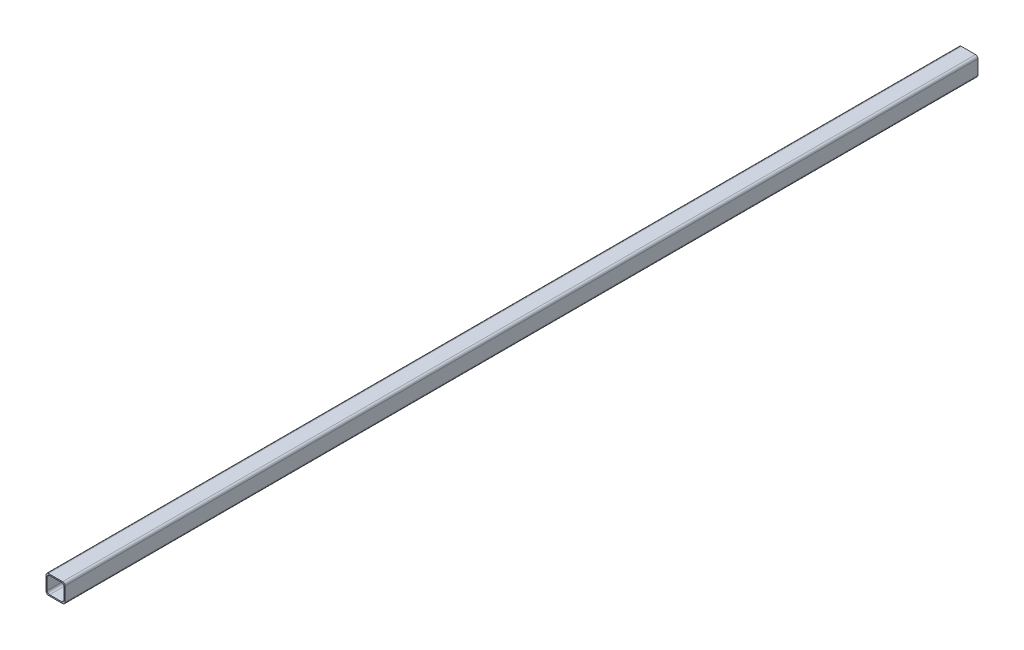
SolidWorks part; units mm, degrees
ref_plane "Front Plane" through (0, 0, 0) normal (0, 0, 1) x (1, 0, 0)
ref_plane "Top Plane" through (0, 0, 0) normal (0, 1, 0) x (1, 0, 0)
ref_plane "Right Plane" through (0, 0, 0) normal (1, 0, 0) x (0, 0, -1)
sketch "Sketch1" plane through (0, 0, 0) normal (0, 0, 1) x (1, 0, 0)
  line L1 (-11.1252, 11.1252) -> (11.1252, 11.1252)
  line L2 (-11.1252, 11.1252) -> (-11.1252, -11.1252)
  line L3 (-11.1252, -11.1252) -> (11.1252, -11.1252)
  line L4 (11.1252, 11.1252) -> (11.1252, -11.1252)
  line L5 (-11.1252, 11.1252) -> (11.1252, -11.1252) construction
  line L6 (-11.1252, -11.1252) -> (11.1252, 11.1252) construction
  line L7 (-12.7, 12.7) -> (12.7, 12.7)
  line L8 (-12.7, 12.7) -> (-12.7, -12.7)
  line L9 (-12.7, -12.7) -> (12.7, -12.7)
  line L10 (12.7, 12.7) -> (12.7, -12.7)
  line L11 (-12.7, 12.7) -> (12.7, -12.7) construction
  line L12 (-12.7, -12.7) -> (12.7, 12.7) construction
  point P0 (0, 0)
  point P6 (0, 0)
  dimension "D1" = 25.4
  dimension "D2" = 1.5748
extrude "Boss-Extrude1" add sketch "Sketch1" along normal mid plane 1219.2
fillet "Fillet1" radius 3.175 8 edges at (11.1252, -11.1252, 0) (-11.1252, -11.1252, 0) (12.7, -12.7, 0) (-12.7, -12.7, 0) (11.1252, 11.1252, 0) (-11.1252, 11.1252, 0) (-12.7, 12.7, 0) (12.7, 12.7, 0)
